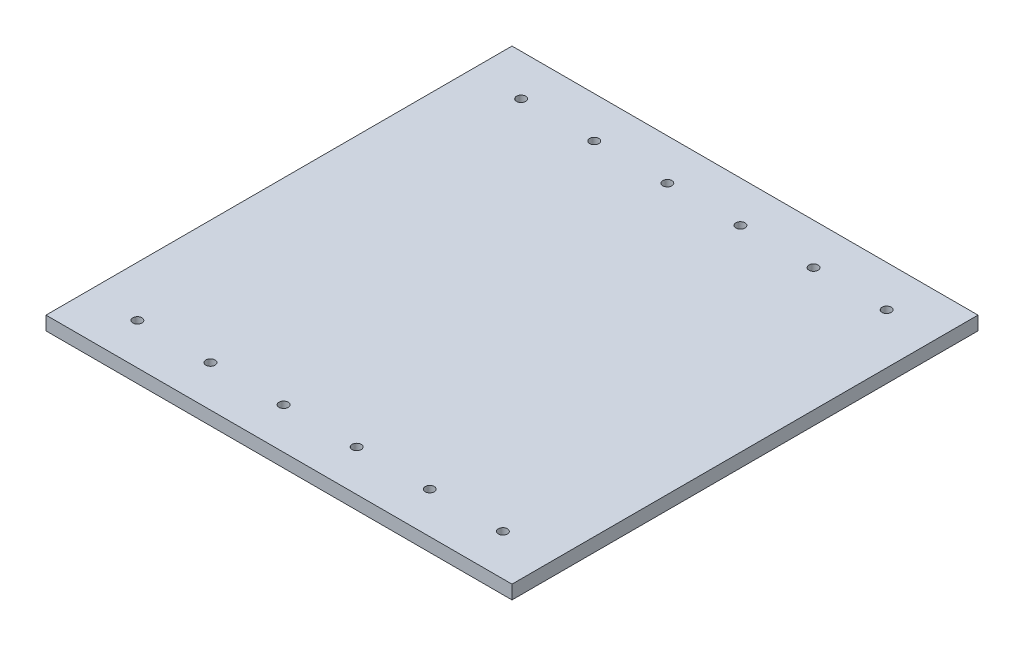
SolidWorks part; units mm, degrees
ref_plane "Front Plane" through (0, 0, 0) normal (0, 0, 1) x (1, 0, 0)
ref_plane "Top Plane" through (0, 0, 0) normal (0, 1, 0) x (1, 0, 0)
ref_plane "Right Plane" through (0, 0, 0) normal (1, 0, 0) x (0, 0, -1)
sketch "Sketch1" plane through (0, 0, 0) normal (0, 1, 0) x (1, 0, 0)
  line L1 (0, 0) -> (647.7, 0)
  line L2 (0, 0) -> (0, -647.7)
  line L3 (0, -647.7) -> (647.7, -647.7)
  line L4 (647.7, 0) -> (647.7, -647.7)
  circle A0 centre (69.85, -57.15) radius 6.35
  circle A1 centre (171.45, -57.15) radius 6.35
  circle A2 centre (273.05, -57.15) radius 6.35
  circle A3 centre (374.65, -57.15) radius 6.35
  circle A4 centre (476.25, -57.15) radius 6.35
  circle A5 centre (577.85, -57.15) radius 6.35
  circle A6 centre (69.85, -590.55) radius 6.35
  circle A7 centre (171.45, -590.55) radius 6.35
  circle A8 centre (273.05, -590.55) radius 6.35
  circle A9 centre (374.65, -590.55) radius 6.35
  circle A10 centre (476.25, -590.55) radius 6.35
  circle A11 centre (577.85, -590.55) radius 6.35
  dimension "D3" = 12.7
  dimension "D4" = 57.15
  dimension "D5" = 69.85
  dimension "D1" = 647.7
  dimension "D2" = 647.7
  dimension "D6" = 6
  dimension "D7" = 2
extrude "Boss-Extrude1" add sketch "Sketch1" along normal blind 19.05
